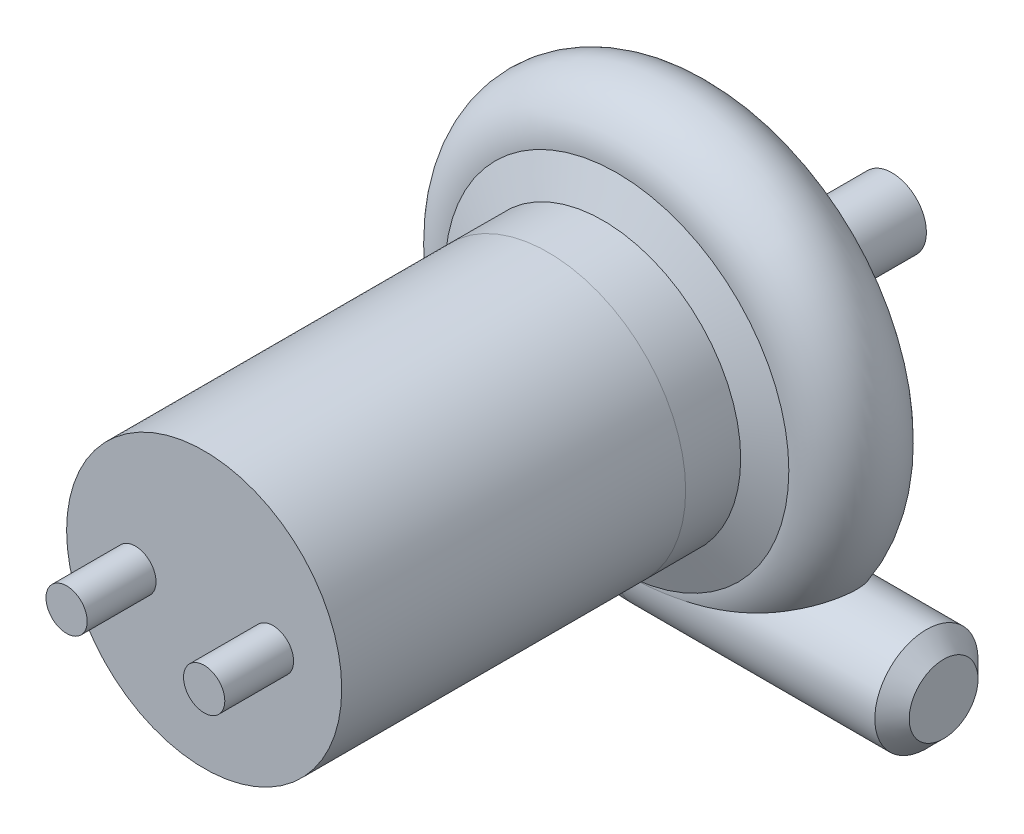
SolidWorks part; units mm, degrees
ref_plane "Front Plane" through (0, 0, 0) normal (0, 0, 1) x (1, 0, 0)
ref_plane "Top Plane" through (0, 0, 0) normal (0, 1, 0) x (1, 0, 0)
ref_plane "Right Plane" through (0, 0, 0) normal (1, 0, 0) x (0, 0, -1)
sketch "Sketch1" plane through (0, 0, 0) normal (0, 0, 1) x (1, 0, 0)
  circle A0 centre (0, 0) radius 20
extrude "Boss-Extrude1" add sketch "Sketch1" along normal blind 50
sketch "Sketch3" plane through (0, 0, 0) normal (1, 0, 0) x (0, 0, -1)
  line L0 (0, 0) -> (0, 20)
  line L1 (0, -20) -> (0, 20) construction
  line L2 (10, 25) -> (25, 25) construction
  line L3 (0, 20) -> (8, 20)
  line L4 (8, 20) -> (10, 25)
  line L5 (25, 25) -> (25, 15)
  line L6 (25, 15) -> (35, 10)
  line L7 (0, 0) -> (50, 0)
  line L8 (50, 0) -> (50, 5)
  line L9 (35, 10) -> (35, 5)
  line L10 (35, 5) -> (50, 5)
  line L11 (-50, 20) -> (-50, -20) construction
  arc A0 (10, 25) -> (25, 25) centre (17.5, 25) cw
  point P16 (17.5, 32.5)
  dimension "D1" = 5
  dimension "D2" = 15
  dimension "D3" = 10
  dimension "D4" = 5
  dimension "D5" = 50
  dimension "D6" = 5
  dimension "D7" = 67.5
  dimension "D8" = 32.5
  dimension "D9" = 32.5
revolve "Revolve1" add sketch "Sketch3" angle 360 about L7
sketch "Sketch4" plane through (0, 0, 0) normal (1, 0, 0) x (0, 0, -1)
  line L0 (10, -25) -> (25, -25) construction
  line L1 (10, 25) -> (10, -25) construction
  line L2 (25, -25) -> (25, 25) construction
  circle A0 centre (17.5, -25) radius 7.5
  dimension "D2" = 15
  dimension "D1" = 15
  dimension "D3" = 25
extrude "Boss-Extrude2" add sketch "Sketch4" along normal blind 40
chamfer "Chamfer1" distance 2.5 angle 45 1 edges at (40, -25, -25)
sketch "Sketch6" plane through (0, 0, 50) normal (0, 0, 1) x (1, 0, 0)
  line L0 (0, 0) -> (20, 0) construction
  line L1 (0, 0) -> (-20, 0) construction
  circle A0 centre (0, 0) radius 20 construction
  circle A1 centre (10, 0) radius 3
  circle A2 centre (-10, 0) radius 3
extrude "Boss-Extrude4" add sketch "Sketch6" along normal blind 10
